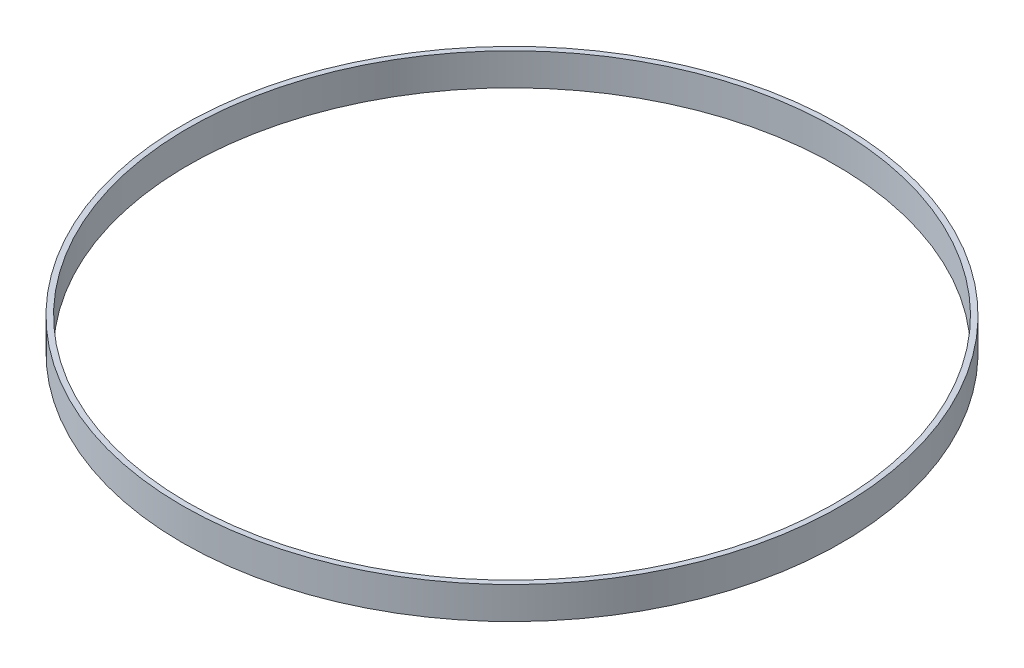
SolidWorks part; units mm, degrees
ref_plane "Front Plane" through (0, 0, 0) normal (0, 0, 1) x (1, 0, 0)
ref_plane "Top Plane" through (0, 0, 0) normal (0, 1, 0) x (1, 0, 0)
ref_plane "Right Plane" through (0, 0, 0) normal (1, 0, 0) x (0, 0, -1)
sketch "Sketch1" plane through (0, 0, 0) normal (0, 1, 0) x (1, 0, 0)
  circle A0 centre (0, 0) radius 96.2025
  circle A1 centre (0, 0) radius 97.79
  dimension "D1" = 195.58
  dimension "D2" = 192.405
extrude "Boss-Extrude1" add sketch "Sketch1" along normal blind 9.525
